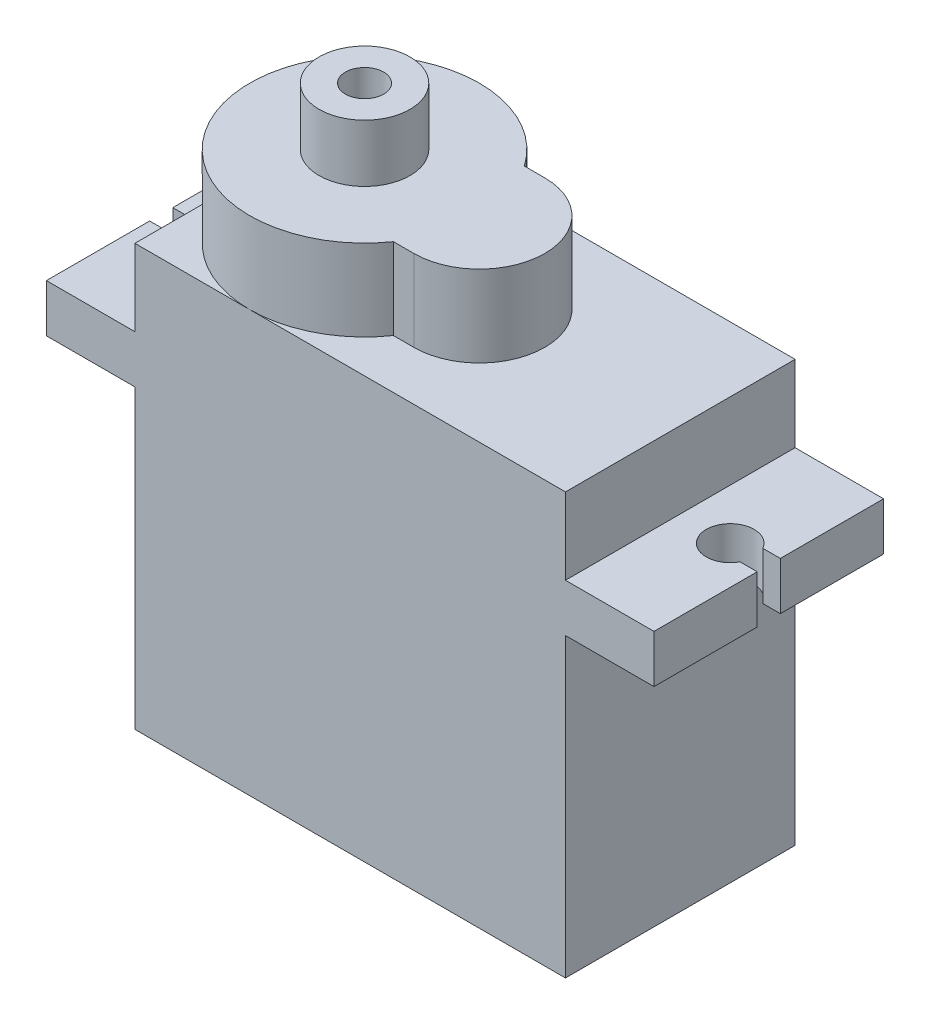
SolidWorks part; units mm, degrees
ref_plane "Front Plane" through (0, 0, 0) normal (0, 0, 1) x (1, 0, 0)
ref_plane "Top Plane" through (0, 0, 0) normal (0, 1, 0) x (1, 0, 0)
ref_plane "Right Plane" through (0, 0, 0) normal (1, 0, 0) x (0, 0, -1)
sketch "Sketch1" plane through (0, 0, 0) normal (0, 1, 0) x (1, 0, 0)
  line L1 (-11.43, -6.096) -> (11.43, -6.096)
  line L2 (-11.43, -6.096) -> (-11.43, 6.096)
  line L3 (-11.43, 6.096) -> (11.43, 6.096)
  line L4 (11.43, -6.096) -> (11.43, 6.096)
  line L5 (-11.43, -6.096) -> (11.43, 6.096) construction
  line L6 (-11.43, 6.096) -> (11.43, -6.096) construction
  point P0 (0, 0)
  dimension "D1" = 22.86
  dimension "D2" = 12.192
extrude "Boss-Extrude1" add sketch "Sketch1" along normal blind 22.352
sketch "Sketch2" plane through (0, 22.352, 0) normal (0, 1, 0) x (1, 0, 0)
  line L0 (11.43, 6.096) -> (-11.43, 6.096) construction
  line L1 (-11.43, -6.096) -> (11.43, -6.096) construction
  line L2 (-11.43, 6.096) -> (-11.43, -6.096) construction
  line L3 (0.762, 3.4758) -> (-0.326, 3.4758)
  line L4 (0.762, -3.4758) -> (-0.326, -3.4758)
  arc A0 (-0.326, 3.4758) -> (-0.326, -3.4758) centre (-5.334, 0) ccw
  arc A1 (0.762, -3.4758) -> (0.762, 3.4758) centre (0.762, 0) ccw
extrude "Boss-Extrude2" add sketch "Sketch2" along normal blind 4.318
sketch "Sketch3" plane through (0, 0, 0) normal (0, -1, 0) x (1, 0, 0)
  line L0 (-11.43, 6.096) -> (11.43, 6.096) construction
  line L1 (-16.129, -6.096) -> (16.129, -6.096)
  line L2 (-16.129, -6.096) -> (-16.129, -0.6135)
  line L3 (-16.129, 6.096) -> (16.129, 6.096)
  line L4 (16.129, -6.096) -> (16.129, -0.6135)
  line L5 (-16.129, -6.096) -> (16.129, 6.096) construction
  line L6 (-16.129, 6.096) -> (16.129, -6.096) construction
  line L7 (-16.129, 0.6135) -> (-15.2182, 0.6135)
  line L8 (-16.129, -0.6135) -> (-15.1994, -0.6135)
  line L9 (-15.6736, 0.6135) -> (-15.6642, -0.6135) construction
  line L10 (-16.129, 0.6135) -> (-16.129, 6.096)
  line L11 (0, -6.7056) -> (0, 6.7056) construction
  line L12 (16.129, 0.6135) -> (15.2182, 0.6135)
  line L13 (16.129, -0.6135) -> (15.1994, -0.6135)
  line L14 (16.129, 0.6135) -> (16.129, 6.096)
  arc A0 (-15.1994, -0.6135) -> (-15.2182, 0.6135) centre (-14.097, 0.017) ccw
  arc A1 (15.1994, -0.6135) -> (15.2182, 0.6135) centre (14.097, 0.017) cw
  point P0 (0, 0)
  point P23 (6.7085, 5.0033)
  dimension "D2" = 2.54
  dimension "D1" = 32.258
  dimension "D3" = 2.032
extrude "Boss-Extrude3" add sketch "Sketch3" against normal blind 2.54 from offset 15.748 offset against normal yes
sketch "Sketch4" plane through (0, 26.67, 0) normal (0, 1, 0) x (1, 0, 0)
  circle A0 centre (-5.334, 0) radius 2.413
  arc A1 (-0.326, 3.4758) -> (-0.326, -3.4758) centre (-5.334, 0) ccw construction
  circle A2 centre (-5.334, 0) radius 1.016
  dimension "D1" = 4.826
  dimension "D2" = 2.032
extrude "Boss-Extrude4" add sketch "Sketch4" along normal blind 3.048
